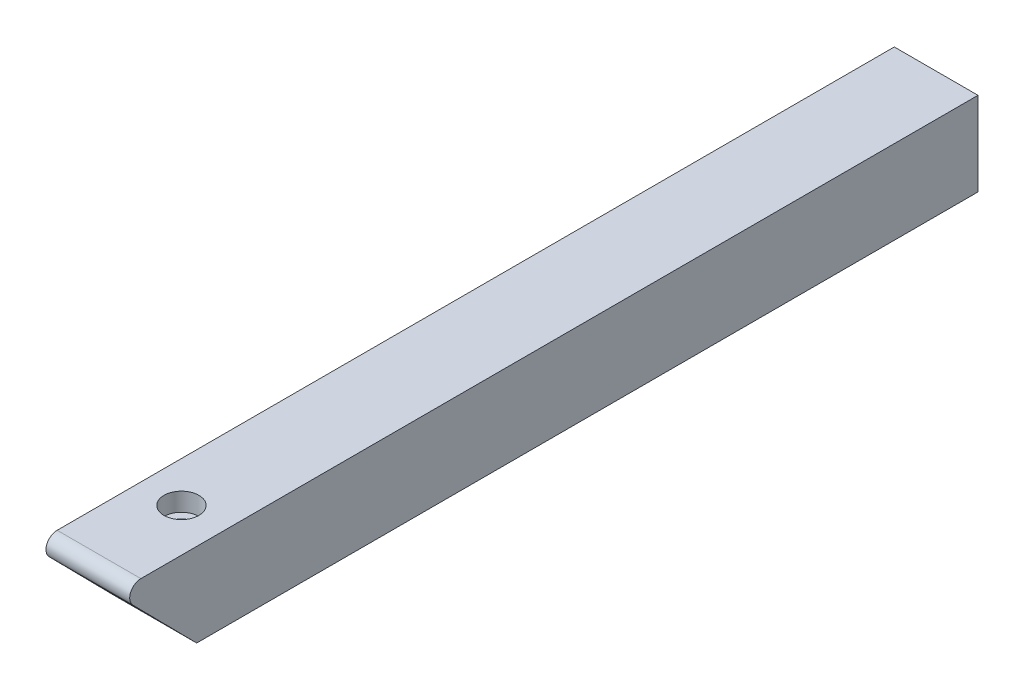
SolidWorks part; units mm, degrees
ref_plane "Front Plane" through (0, 0, 0) normal (0, 0, 1) x (1, 0, 0)
ref_plane "Top Plane" through (0, 0, 0) normal (0, 1, 0) x (1, 0, 0)
ref_plane "Right Plane" through (0, 0, 0) normal (1, 0, 0) x (0, 0, -1)
sketch "Sketch1" plane through (0, 0, 0) normal (0, 0, 1) x (1, 0, 0)
  line L1 (0, 0) -> (19.05, 0)
  line L2 (0, 0) -> (0, 19.05)
  line L3 (0, 19.05) -> (19.05, 19.05)
  line L4 (19.05, 0) -> (19.05, 19.05)
  dimension "D1" = 19.05
  dimension "D2" = 19.05
extrude "Boss-Extrude1" add sketch "Sketch1" along normal blind 177.8
sketch "Sketch2" plane through (19.05, 0, 0) normal (1, 0, 0) x (0, 0, -1)
  line L0 (-177.8, 19.05) -> (-190.5, 19.05)
  line L1 (-192.3094, 14.7274) -> (-177.8, 0)
  line L6 (0, 0) -> (0, 19.05)
  line L7 (0, 19.05) -> (-177.8, 19.05)
  line L8 (-177.8, 19.05) -> (-177.8, 0)
  line L9 (-177.8, 0) -> (0, 0)
  line L12 (-177.8, 19.05) -> (-177.8, 0)
  arc A0 (-190.5, 19.05) -> (-192.3094, 14.7274) centre (-190.5, 16.51) ccw
  dimension "D1" = 2.54
  dimension "D3" = 12.7
  dimension "D2" = 0
extrude "Boss-Extrude2" add sketch "Sketch2" against normal up to surface (19.05 mm away) up to face at (0, 9.525, 88.9)
hole_wizard "CBORE for #8 Socket Head Cap Screw1" positions "3DSketch1" profile "Sketch3" counterbore size "#8" standard "ANSI Inch" end condition up to next
sketch3d "3DSketch1"
  line L0 (0, 19.05, 190.5) -> (19.05, 19.05, 190.5) construction
  point P0 (9.2361, 19.05, 171.45)
  dimension "D1" = 19.05
sketch "Sketch3" plane through (9.2361, 19.05, 171.45) normal (1, 0, 0) x (0, 0, 1)
  line L0 (0, 0) -> (0, 19.05)
  line L1 (0, 19.05) -> (2.1526, 19.05)
  line L3 (2.1526, 19.05) -> (2.1527, 4.1656)
  line L4 (2.1527, 4.1656) -> (3.9688, 4.1656)
  line L5 (3.9688, 4.1656) -> (3.9688, 0)
  line L7 (3.9688, 0) -> (0, 0)
  line L11 (0, -6.35) -> (0, 107.95) construction
  dimension "Thru Hole Dia." = 4.3053
  dimension "Thru Hole Depth" = 19.05
  dimension "C'Bore Dia." = 7.9375
  dimension "C'Bore Depth" = 4.1656
equation "\"D2@Sketch1\"=\"D1@Sketch1\""
